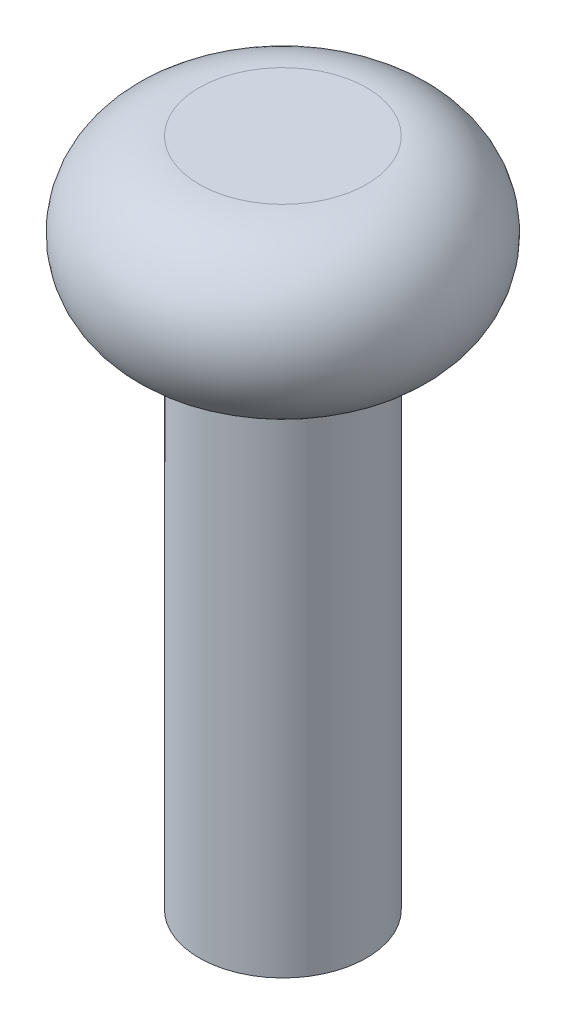
SolidWorks part; units mm, degrees
ref_plane "Front Plane" through (0, 0, 0) normal (0, 0, 1) x (1, 0, 0)
ref_plane "Top Plane" through (0, 0, 0) normal (0, 1, 0) x (1, 0, 0)
ref_plane "Right Plane" through (0, 0, 0) normal (1, 0, 0) x (0, 0, -1)
sketch "Sketch1" plane through (0, 0, 0) normal (0, 0, 1) x (1, 0, 0)
  line L0 (0, 0) -> (0, 10)
  line L2 (0, 0) -> (0, -30)
  line L3 (0, -30) -> (5, -30)
  line L4 (5, 0) -> (5, -30)
  line L6 (5, 10) -> (0, 10)
  arc A1 (5, 0) -> (5, 10) centre (5, 5) ccw
  dimension "D2" = 5
  dimension "D1" = 5
revolve "Revolve1" add sketch "Sketch1" angle 360 about L2
